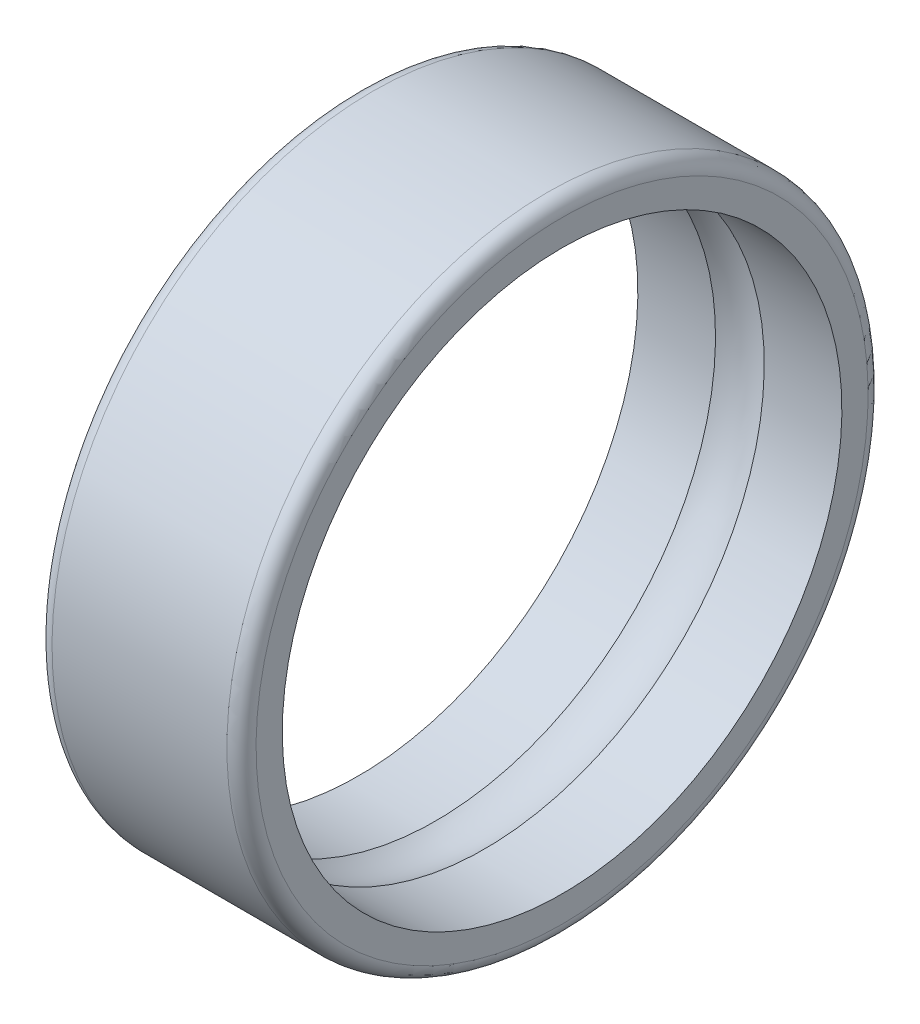
SolidWorks part; units mm, degrees
ref_plane "Front Plane" through (0, 0, 0) normal (0, 0, 1) x (1, 0, 0)
ref_plane "Top Plane" through (0, 0, 0) normal (0, 1, 0) x (1, 0, 0)
ref_plane "Right Plane" through (0, 0, 0) normal (1, 0, 0) x (0, 0, -1)
sketch "Sketch2" plane through (0, 0, 0) normal (0, 0, 1) x (1, 0, 0)
  line L0 (23.6602, 0) -> (-21.7547, 0) construction
  line L1 (3.5, 11) -> (-3.5, 11)
  line L2 (3.5, 11) -> (3.5, 9.6)
  line L3 (3.5, 9.6) -> (-3.5, 9.6)
  line L4 (-3.5, 9.6) -> (-3.5, 11)
  line L5 (3.5, 6.05) -> (3.5, 4)
  line L6 (3.5, 4) -> (-3.5, 4)
  line L7 (-3.5, 4) -> (-3.5, 6.05)
  line L8 (-3.5, 6.05) -> (3.5, 6.05)
  circle A0 centre (0, 7.8) radius 1.9845
  point P9 (0, 11)
  dimension "D1" = 1.75
  dimension "Ball Bearing Size" = 3.969
  dimension "Bearing Width" = 7
  dimension "Inner Casing Inner" = 4
  dimension "Inner Casing Outter" = 6.05
  dimension "Outter Casing Inner" = 9.6
  dimension "Outter Case Outter" = 11
revolve "Revolve1" add sketch "Sketch2" angle 360 about L0
fillet "Fillet1" radius 0.5 2 edges at (-3.5, 11, 0) (3.5, 11, 0)
equation "\"Motor Width\"= 42.3'eg: For stepper motor Nema 17 = 42.3mm"
equation "\"Motor Hole Config Width\"= 31'eg: For stepper motor Nema 17 = 31"
equation "\"Mounting Hole Diameter\"= 3'eg: For Nema 17 3mm"
equation "\"Motor Depth\"= 50'eg: For Nema 17 50mm"
equation "\"Exposed Shaft Length\"= 22'eg: For Nema 17 22mm"
equation "\"Shaft Seround Depthr\"= 2'eg: For Nema 17 2mm"
equation "\"Shaft Diameter\"= 5'eg: For Nema 17 5mm"
equation "\"Top/Bottom Casing Depth\"= 10'Guess"
equation "\"Mid Casing Depth\"= \"Motor Depth\" - 2 * ( \"Top/Bottom Casing Depth\" )"
equation "\"Bearing Outter Diameter\"= 22' From Spec 608z = 22mm"
equation "\"Shaft Clearance Hole\"= \"Shaft Diameter\"+1.5'Guess"
equation "\"Bearing Ball Size\"= 3.969'From Spec"
equation "\"Bearing Inner Case Inner Diameter\"= 8'From Spec"
equation "\"Bearing Inner Case Outter Diameter\"= 12.1'From Spec"
equation "\"Bearing Outter Case Inner Diameter\"= 19.2'From Spec"
equation "\"Bearing Width\"= 7'From Spec"
equation "\"Bearing Width@Sketch2\"=\"Bearing Width\""
equation "\"Inner Casing Inner@Sketch2\"=\"Bearing Inner Case Inner Diameter\"/2"
equation "\"Inner Casing Outter@Sketch2\"=\"Bearing Inner Case Outter Diameter\"/2"
equation "\"Outter Casing Inner@Sketch2\"=\"Bearing Outter Case Inner Diameter\"/2"
equation "\"Outter Case Outter@Sketch2\"=\"Bearing Outter Diameter\"/2"
equation "\"Ball Bearing Size@Sketch2\"=\"Bearing Ball Size\""
